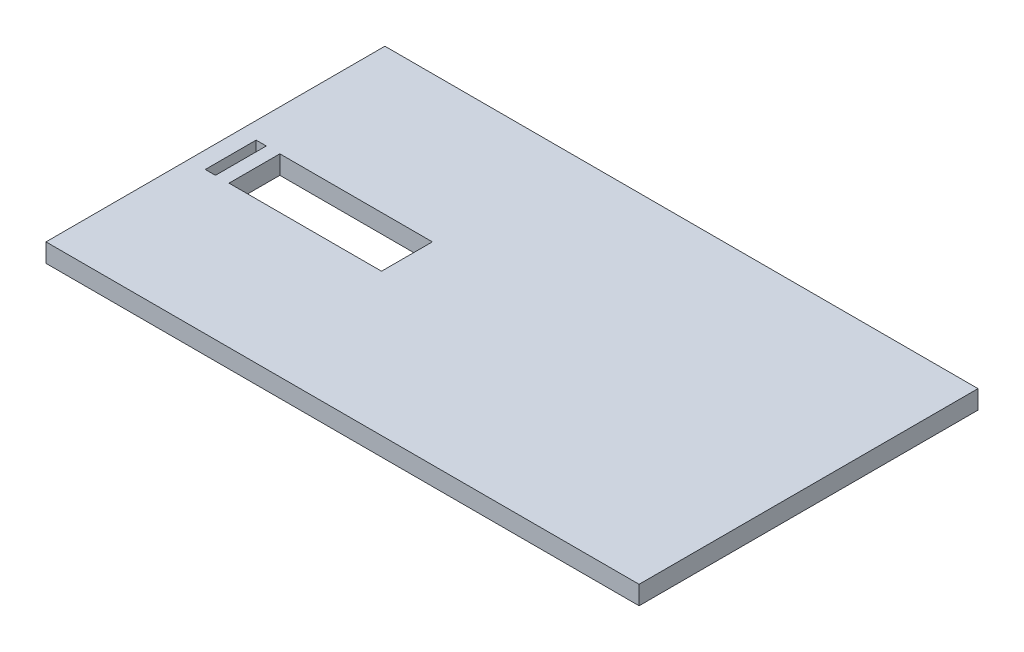
SolidWorks part; units mm, degrees
ref_plane "Front Plane" through (0, 0, 0) normal (0, 0, 1) x (1, 0, 0)
ref_plane "Top Plane" through (0, 0, 0) normal (0, 1, 0) x (1, 0, 0)
ref_plane "Right Plane" through (0, 0, 0) normal (1, 0, 0) x (0, 0, -1)
sketch "Sketch1" plane through (0, 0, 0) normal (0, 1, 0) x (1, 0, 0)
  line L1 (-142.3913, 94.0217) -> (207.6087, 94.0217)
  line L2 (-142.3913, 94.0217) -> (-142.3913, -105.9783)
  line L3 (-142.3913, -105.9783) -> (207.6087, -105.9783)
  line L4 (207.6087, 94.0217) -> (207.6087, -105.9783)
  dimension "D1" = 350
  dimension "D2" = 200
extrude "Boss-Extrude1" add sketch "Sketch1" along normal blind 11
sketch "Sketch2" plane through (0, 11, 0) normal (0, 1, 0) x (1, 0, 0)
  line L0 (-142.3913, -5.9783) -> (216.2748, -5.9783) construction
  line L1 (-142.3913, 94.0217) -> (-142.3913, -105.9783) construction
  line L2 (-132.3913, 8.0217) -> (-126.3913, 8.0217) construction
  line L4 (-118.3913, 8.0217) -> (-28.3913, 8.0217) construction
  line L5 (-118.3913, 8.0217) -> (-28.3913, 8.0217)
  line L6 (-118.3913, 8.0217) -> (-118.3913, -21.9783)
  line L7 (-118.3913, -21.9783) -> (-28.3913, -21.9783)
  line L8 (-28.3913, 8.0217) -> (-28.3913, -21.9783)
  line L9 (-132.3913, 8.0217) -> (-126.3913, 8.0217)
  line L10 (-132.3913, 8.0217) -> (-132.3913, -21.9783)
  line L11 (-132.3913, -21.9783) -> (-126.3913, -21.9783)
  line L12 (-126.3913, 8.0217) -> (-126.3913, -21.9783)
  dimension "D1" = 14
  dimension "D2" = 30
  dimension "D3" = 30
  dimension "D4" = 90
  dimension "D5" = 6
  dimension "D6" = 24
  dimension "D7" = 10
extrude "Cut-Extrude1" cut sketch "Sketch2" against normal through all and the other way through all
